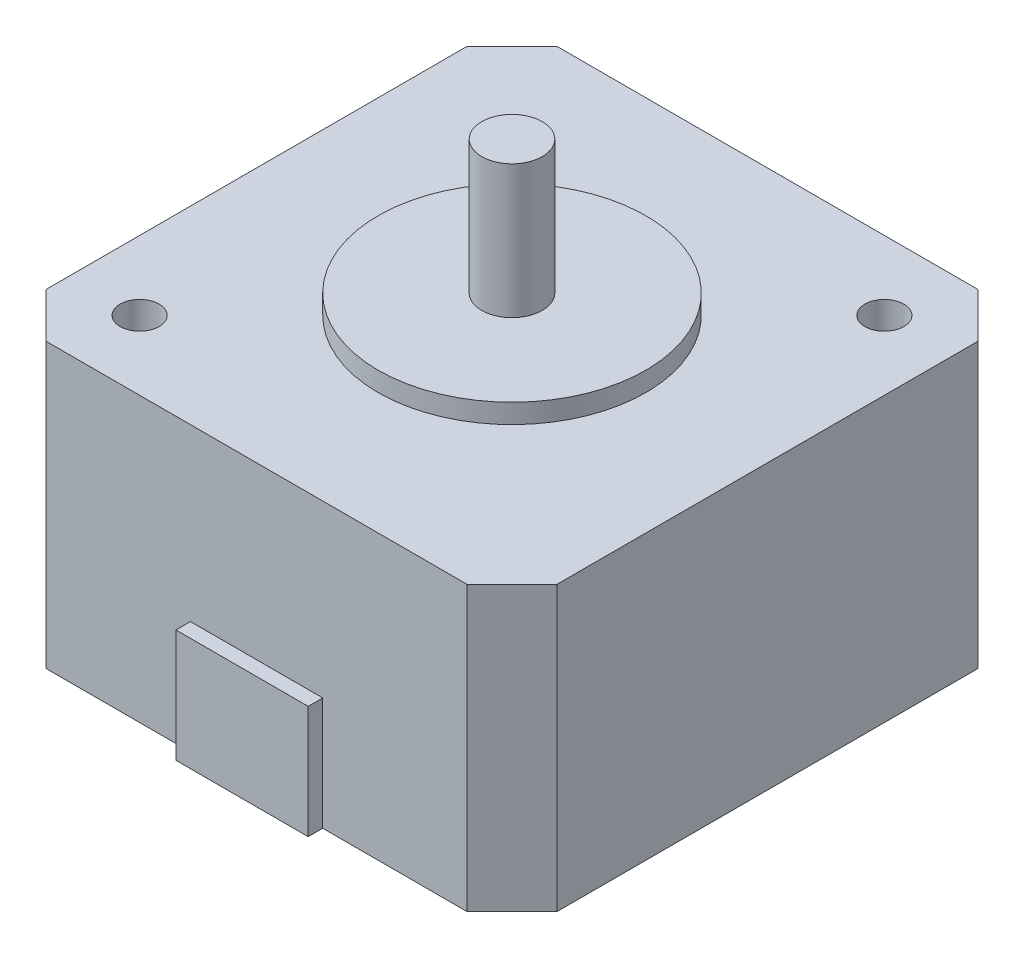
SolidWorks part; units mm, degrees
ref_plane "Front Plane" through (0, 0, 0) normal (0, 0, 1) x (1, 0, 0)
ref_plane "Top Plane" through (0, 0, 0) normal (0, 1, 0) x (1, 0, 0)
ref_plane "Right Plane" through (0, 0, 0) normal (1, 0, 0) x (0, 0, -1)
sketch "Sketch1" plane through (0, 0, 0) normal (0, 1, 0) x (1, 0, 0)
  line L0 (0, 21.085) -> (0, -21.085) construction
  line L1 (-17.385, 21.085) -> (17.385, 21.085)
  line L2 (-21.085, 17.385) -> (-21.085, -17.385)
  line L3 (-17.385, -21.085) -> (17.385, -21.085)
  line L4 (21.085, 17.385) -> (21.085, -17.385)
  line L5 (17.385, 21.085) -> (21.085, 17.385)
  line L6 (-21.085, 17.385) -> (-17.385, 21.085)
  line L7 (17.385, -21.085) -> (21.085, -17.385)
  line L8 (-21.085, -17.385) -> (-17.385, -21.085)
  point P0 (-21.085, 21.085)
  point P1 (21.085, -21.085)
  point P2 (-21.085, -21.085)
  point P3 (21.085, 21.085)
  point P6 (0, 0)
  dimension "D1" = 42.17
  dimension "D2" = 42.17
extrude "Boss-Extrude1" add sketch "Sketch1" along normal blind 23.4
sketch "Sketch2" plane through (0, 0, 21.085) normal (0, 0, 1) x (1, 0, 0)
  line L0 (-17.385, 0) -> (17.385, 0) construction
  line L1 (-5.46, 9.32) -> (5.46, 9.32)
  line L2 (-5.46, 9.32) -> (-5.46, 0)
  line L3 (-5.46, 0) -> (5.46, 0)
  line L4 (5.46, 9.32) -> (5.46, 0)
  point P6 (0, 0)
  dimension "D1" = 10.92
  dimension "D2" = 9.32
extrude "Boss-Extrude2" add sketch "Sketch2" along normal blind 1.2
sketch "Sketch3" plane through (0, 23.4, 0) normal (0, 1, 0) x (1, 0, 0)
  line L0 (0, 15.37) -> (0, -15.37) construction
  line L1 (0, -15.37) -> (-15.37, -15.37) construction
  line L2 (0, 15.37) -> (15.37, 15.37) construction
  circle A1 centre (-15.37, -15.37) radius 1.61
  circle A2 centre (15.37, 15.37) radius 1.61
  dimension "D5" = 3.22
  dimension "D6" = 3.22
  dimension "D1" = 30.74
  dimension "D2" = 15.37
  dimension "D3" = 15.37
extrude "Cut-Extrude1" cut sketch "Sketch3" against normal through all
sketch "Sketch4" plane through (0, 23.4, 0) normal (0, 1, 0) x (1, 0, 0)
  circle A0 centre (0, 0) radius 11.05
  dimension "D1" = 22.1
extrude "Boss-Extrude3" add sketch "Sketch4" along normal blind 1.6
sketch "Sketch5" plane through (0, 25, 0) normal (0, 1, 0) x (1, 0, 0)
  circle A0 centre (0, 0) radius 2.5
  dimension "D1" = 5
extrude "Boss-Extrude4" add sketch "Sketch5" along normal blind 11
